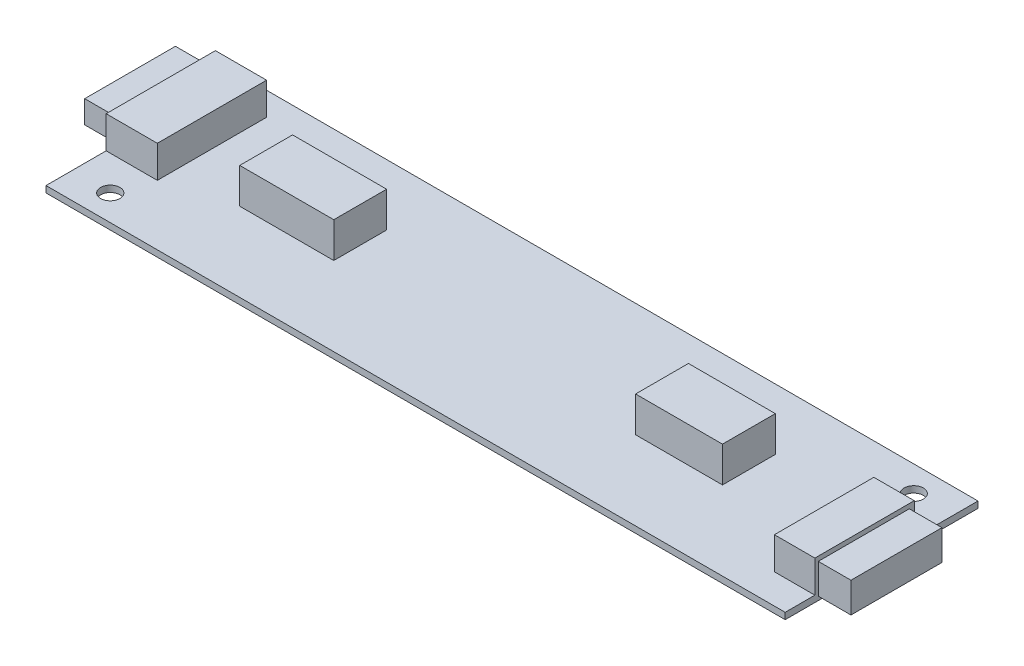
SolidWorks part; units mm, degrees
ref_plane "Front Plane" through (0, 0, 0) normal (0, 0, 1) x (1, 0, 0)
ref_plane "Top Plane" through (0, 0, 0) normal (0, 1, 0) x (1, 0, 0)
ref_plane "Right Plane" through (0, 0, 0) normal (1, 0, 0) x (0, 0, -1)
sketch "Sketch1" plane through (0, 0, 0) normal (0, 1, 0) x (1, 0, 0)
  line L1 (0, 0) -> (115, 0)
  line L2 (0, 0) -> (0, -30)
  line L3 (0, -30) -> (115, -30)
  line L4 (115, 0) -> (115, -30)
  dimension "D1" = 115
  dimension "D2" = 30
extrude "Extrude1" add sketch "Sketch1" along normal blind 1
sketch "Sketch2" plane through (0, 1, 0) normal (0, 1, 0) x (-1, 0, 0)
  line L0 (0, 30) -> (-115, 30) construction
  line L1 (0, 0) -> (0, 30) construction
  circle A0 centre (-109, 4) radius 1.5
  circle A1 centre (-6, 26) radius 1.5
  dimension "D1" = 3
  dimension "D2" = 3
  dimension "D3" = 4
  dimension "D4" = 6
  dimension "D5" = 26
  dimension "D6" = 109
extrude "mount holes - cut" cut sketch "Sketch2" against normal blind 1
sketch "Sketch4" plane through (0, 1, 0) normal (0, 1, 0) x (-1, 0, 0)
  line L1 (-92.9629, 9.4959) -> (-79.4466, 9.4959)
  line L2 (-92.9629, 9.4959) -> (-92.9629, 17.7172)
  line L3 (-92.9629, 17.7172) -> (-79.4466, 17.7172)
  line L4 (-79.4466, 9.4959) -> (-79.4466, 17.7172)
  line L5 (-32.4879, 9.4959) -> (-17.8568, 9.4959)
  line L6 (-32.4879, 9.4959) -> (-32.4879, 17.7172)
  line L7 (-32.4879, 17.7172) -> (-17.8568, 17.7172)
  line L8 (-17.8568, 9.4959) -> (-17.8568, 17.7172)
extrude "inductors" add sketch "Sketch4" along normal blind 5.5
sketch "Sketch5" plane through (0, 1, 0) normal (0, 1, 0) x (-1, 0, 0)
  line L0 (-115, 30) -> (-115, 0) construction
  line L1 (-115, 9.914) -> (-108.7087, 9.914)
  line L2 (-115, 9.914) -> (-115, 25.3811)
  line L3 (-115, 25.3811) -> (-108.7087, 25.3811)
  line L4 (-108.7087, 9.914) -> (-108.7087, 25.3811)
  line L5 (0, 0) -> (0, 30) construction
  line L6 (-7.9635, 3.6435) -> (0, 3.6435)
  line L7 (-7.9635, 3.6435) -> (-7.9635, 20.6434)
  line L8 (-7.9635, 20.6434) -> (0, 20.6434)
  line L9 (0, 3.6435) -> (0, 20.6434)
extrude "ccfl conn" add sketch "Sketch5" along normal blind 5
sketch "Sketch6" plane through (115, 0, 0) normal (1, 0, 0) x (0, 0, -1)
  line L1 (-24.8452, 5.2864) -> (-10.6883, 5.2864)
  line L2 (-24.8452, 5.2864) -> (-24.8452, 0.5956)
  line L3 (-24.8452, 0.5956) -> (-10.6883, 0.5956)
  line L4 (-10.6883, 5.2864) -> (-10.6883, 0.5956)
extrude "mate and wire stick-out 1" add sketch "Sketch6" along normal blind 5.08
sketch "Sketch7" plane through (0, 0, 0) normal (-1, 0, 0) x (0, 0, 1)
  line L1 (4.7831, 4.6156) -> (18.9002, 4.6156)
  line L2 (4.7831, 4.6156) -> (4.7831, 1.0835)
  line L3 (4.7831, 1.0835) -> (18.9002, 1.0835)
  line L4 (18.9002, 4.6156) -> (18.9002, 1.0835)
extrude "mate and wire stick-out 2" add sketch "Sketch7" along normal blind 5.08
